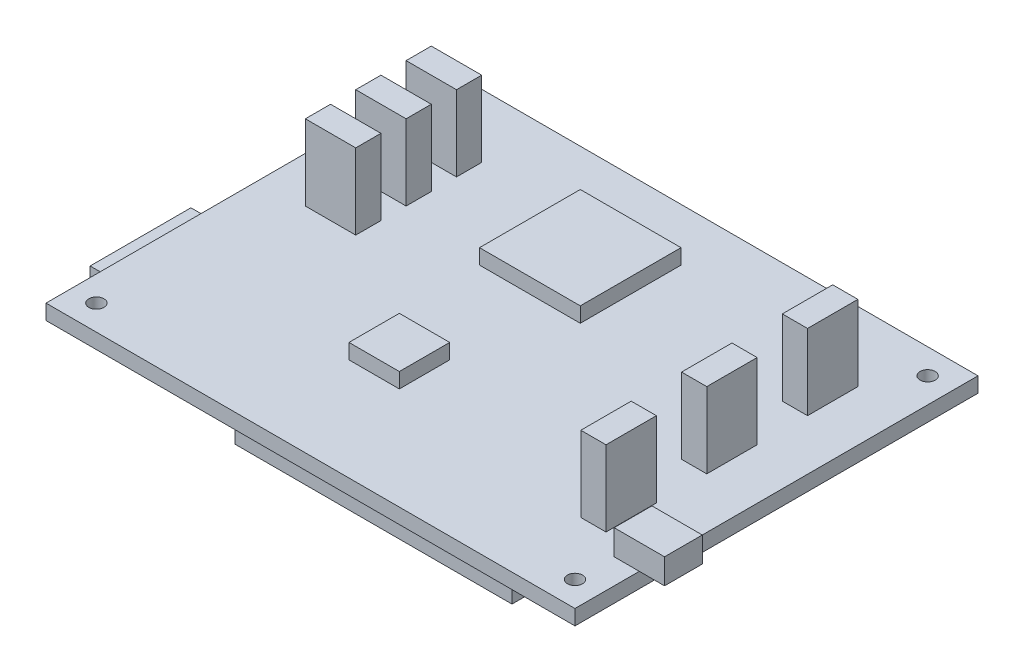
SolidWorks part; units mm, degrees
ref_plane "Face" through (0, 0, 0) normal (0, 0, 1) x (1, 0, 0)
ref_plane "Dessus" through (0, 0, 0) normal (0, 1, 0) x (1, 0, 0)
ref_plane "Droite" through (0, 0, 0) normal (1, 0, 0) x (0, 0, -1)
sketch "Esquisse1" plane through (0, 0, 0) normal (0, 1, 0) x (1, 0, 0)
  line L0 (52.5, 80) -> (52.5, 0) construction
  line L1 (0, 0) -> (105, 0)
  line L2 (0, 0) -> (0, 80)
  line L3 (0, 80) -> (105, 80)
  line L4 (105, 0) -> (105, 80)
  line L5 (0, 40) -> (105, 40) construction
  circle A0 centre (5, 75) radius 1.5
  circle A1 centre (100, 75) radius 1.5
  circle A2 centre (100, 5) radius 1.5
  circle A3 centre (5, 5) radius 1.5
  dimension "D3" = 3
  dimension "D1" = 105
  dimension "D2" = 80
  dimension "D4" = 5
  dimension "D5" = 5
extrude "Extrusion1" add sketch "Esquisse1" along normal blind 3
sketch "Esquisse2" plane through (0, 3, 0) normal (0, 1, 0) x (1, 0, 0)
  line L1 (36.4987, 49.5537) -> (56.4987, 49.5537)
  line L2 (36.4987, 49.5537) -> (36.4987, 69.5537)
  line L3 (36.4987, 69.5537) -> (56.4987, 69.5537)
  line L4 (56.4987, 49.5537) -> (56.4987, 69.5537)
  line L5 (39.8307, 30.3059) -> (49.8307, 30.3059)
  line L6 (39.8307, 30.3059) -> (39.8307, 20.3059)
  line L7 (39.8307, 20.3059) -> (49.8307, 20.3059)
  line L8 (49.8307, 30.3059) -> (49.8307, 20.3059)
  dimension "D1" = 20
  dimension "D2" = 10
extrude "Extrusion2" add sketch "Esquisse2" along normal blind 3
sketch "Esquisse3" plane through (0, 3, 0) normal (0, 1, 0) x (1, 0, 0)
  line L0 (89.939, 66.2217) -> (94.939, 66.2217)
  line L1 (9.058, 67.4227) -> (19.058, 67.4227)
  line L2 (9.058, 67.4227) -> (9.058, 62.4227)
  line L3 (9.058, 62.4227) -> (19.058, 62.4227)
  line L4 (19.058, 67.4227) -> (19.058, 62.4227)
  line L5 (9.058, 57.4227) -> (19.058, 57.4227)
  line L6 (9.058, 57.4227) -> (9.058, 52.4227)
  line L7 (9.058, 52.4227) -> (19.058, 52.4227)
  line L8 (19.058, 57.4227) -> (19.058, 52.4227)
  line L9 (9.058, 47.4227) -> (19.058, 47.4227)
  line L10 (9.058, 47.4227) -> (9.058, 42.4227)
  line L11 (9.058, 42.4227) -> (19.058, 42.4227)
  line L12 (19.058, 47.4227) -> (19.058, 42.4227)
  line L13 (89.939, 66.2217) -> (89.939, 56.2217)
  line L14 (89.939, 56.2217) -> (94.939, 56.2217)
  line L15 (94.939, 66.2217) -> (94.939, 56.2217)
  line L16 (89.939, 46.2217) -> (94.939, 46.2217)
  line L17 (89.939, 46.2217) -> (89.939, 36.2217)
  line L18 (89.939, 36.2217) -> (94.939, 36.2217)
  line L19 (94.939, 46.2217) -> (94.939, 36.2217)
  line L20 (89.939, 26.2217) -> (94.939, 26.2217)
  line L21 (89.939, 26.2217) -> (89.939, 16.2217)
  line L22 (89.939, 16.2217) -> (94.939, 16.2217)
  line L23 (94.939, 26.2217) -> (94.939, 16.2217)
  line L24 (9.058, 67.4227) -> (9.058, 42.4227) construction
  line L25 (94.939, 66.2217) -> (94.939, 16.2217) construction
  dimension "D1" = 5
  dimension "D2" = 10
  dimension "D3" = 5
  dimension "D4" = 5
  dimension "D5" = 10
  dimension "D6" = 5
  dimension "D7" = 10
  dimension "D8" = 10
extrude "Extrusion3" add sketch "Esquisse3" along normal blind 15
sketch "Esquisse4" plane through (0, 0, 0) normal (0, -1, 0) x (1, 0, 0)
  line L0 (0, -40) -> (105, -40) construction
  line L1 (35, -2.5) -> (90, -2.5)
  line L2 (35, -2.5) -> (35, -7.5)
  line L3 (35, -7.5) -> (90, -7.5)
  line L4 (90, -2.5) -> (90, -7.5)
  line L5 (90, -77.5) -> (90, -72.5)
  line L6 (35, -72.5) -> (90, -72.5)
  line L7 (35, -77.5) -> (35, -72.5)
  line L8 (35, -77.5) -> (90, -77.5)
  line L9 (0, -80) -> (0, 0) construction
  line L10 (105, 0) -> (105, -80) construction
  dimension "D1" = 32.5
  dimension "D2" = 5
  dimension "D3" = 55
  dimension "D4" = 15
extrude "Extrusion4" add sketch "Esquisse4" along normal blind 5
sketch "Esquisse5" plane through (0, 0, 0) normal (0, -1, 0) x (1, 0, 0)
  line L1 (-5, -13.7613) -> (25, -13.7613)
  line L2 (-5, -13.7613) -> (-5, -33.7613)
  line L3 (-5, -33.7613) -> (25, -33.7613)
  line L4 (25, -13.7613) -> (25, -33.7613)
  line L5 (0, -80) -> (0, 0) construction
  dimension "D1" = 20
  dimension "D2" = 30
  dimension "D3" = 5
extrude "Extrusion5" add sketch "Esquisse5" along normal blind 3
sketch "Esquisse6" plane through (0, 3, 0) normal (0, 1, 0) x (1, 0, 0)
  line L0 (105, 0) -> (105, 80) construction
  line L1 (100, 12.775) -> (110, 12.775)
  line L2 (100, 12.775) -> (100, 20.275)
  line L3 (100, 20.275) -> (110, 20.275)
  line L4 (110, 12.775) -> (110, 20.275)
  dimension "D1" = 7.5
  dimension "D2" = 5
  dimension "D3" = 5
extrude "Extrusion6" add sketch "Esquisse6" along normal blind 5
